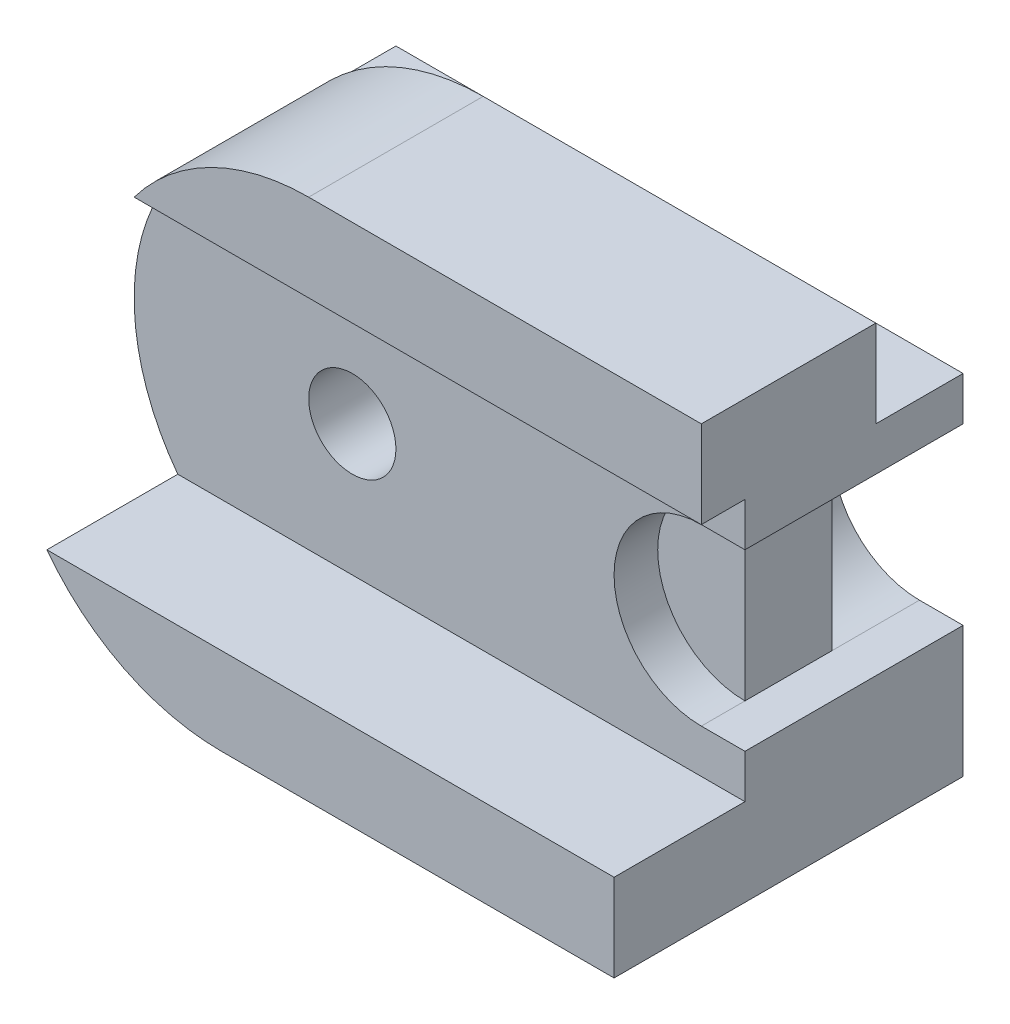
SolidWorks part; units mm, degrees
ref_plane "Front Plane" through (0, 0, 0) normal (0, 0, 1) x (1, 0, 0)
ref_plane "Top Plane" through (0, 0, 0) normal (0, 1, 0) x (1, 0, 0)
ref_plane "Right Plane" through (0, 0, 0) normal (1, 0, 0) x (0, 0, -1)
sketch "Sketch1" plane through (0, 0, 0) normal (0, 0, 1) x (1, 0, 0)
  line L0 (0, 50) -> (90, 50)
  line L1 (90, 50) -> (90, 20)
  line L2 (90, -20) -> (90, -50)
  line L3 (0, -50) -> (90, -50)
  line L4 (90, 20) -> (80, 20)
  line L5 (90, -20) -> (80, -20)
  arc A0 (0, 50) -> (0, -50) centre (0, 0) ccw
  arc A1 (80, 20) -> (80, -20) centre (80, 0) ccw
  dimension "D1" = 100
  dimension "D2" = 90
  dimension "D4" = 10
  dimension "D7" = 20
  dimension "D3" = 90
  dimension "D5" = 10
  dimension "D6" = 10
  dimension "D8" = 30
  dimension "D9" = 30
extrude "Boss-Extrude2" add sketch "Sketch1" along normal blind 80 contours A1 L4 L1 L0 A0 L3 L2 L5
sketch "Sketch8" plane through (90, 0, 0) normal (1, 0, 0) x (0, 0, -1)
  line L1 (0, 50) -> (-20, 50)
  line L2 (0, 50) -> (0, 30)
  line L3 (0, 30) -> (-20, 30)
  line L4 (-20, 50) -> (-20, 30)
  dimension "D1" = 20
  dimension "D2" = 20
extrude "Cut-Extrude5" cut sketch "Sketch8" against normal blind 205
ref_plane "Plane2" through (-50, 0, 0) normal (1, 0, 0) x (0, 0, -1)
sketch "Sketch9" plane through (-50, 0, 0) normal (1, 0, 0) x (0, 0, -1)
  line L1 (-80, 30) -> (-50, 30)
  line L2 (-80, 30) -> (-80, -30)
  line L3 (-80, -30) -> (-50, -30)
  line L4 (-50, 30) -> (-50, -30)
  dimension "D1" = 30
  dimension "D2" = 50
  dimension "D3" = 60
  dimension "D4" = 20
extrude "Cut-Extrude6" cut sketch "Sketch9" along normal blind 205
sketch "Sketch10" plane through (90, 0, 0) normal (1, 0, 0) x (0, 0, -1)
  line L1 (-80, 50) -> (-60, 50)
  line L2 (-80, 50) -> (-80, 30)
  line L3 (-80, 30) -> (-60, 30)
  line L4 (-60, 50) -> (-60, 30)
  dimension "D1" = 20
  dimension "D2" = 20
extrude "Cut-Extrude8" cut sketch "Sketch10" against normal blind 150
sketch "Sketch13" plane through (0, 0, 50) normal (0, 0, 1) x (1, 0, 0)
  circle A0 centre (0, 0) radius 10
  dimension "D1" = 20
extrude "Cut-Extrude9" cut sketch "Sketch13" against normal blind 150
sketch "Sketch14" plane through (0, 0, 0) normal (0, 0, -1) x (-1, 0, 0)
  line L0 (-90, -20) -> (-80, -20) construction
  line L1 (-80, 20) -> (-80, -20)
  arc A0 (-80, 20) -> (-80, -20) centre (-80, 0) cw
extrude "Boss-Extrude5" add sketch "Sketch14" against normal blind 40
sketch "Sketch15" plane through (0, 0, 0) normal (0, 0, -1) x (-1, 0, 0)
  line L0 (-80, 20) -> (-80, -20) construction
  line L1 (-80, 20) -> (-80, -20)
  arc A0 (-80, 20) -> (-80, -20) centre (-80, 0) cw
extrude "Cut-Extrude10" cut sketch "Sketch15" against normal blind 20
sketch "Sketch16" plane through (0, 0, 0) normal (0, 0, -1) x (-1, 0, 0)
  line L0 (-40, 30) -> (-0.001, 30)
  line L1 (40, 30) -> (-90, 30) construction
  line L2 (-0.001, 30) -> (0, 49.999)
  line L3 (-90, 30) -> (-90, 50) construction
  line L4 (-0.001, 30) -> (-0.001, -49.999)
  line L5 (-0.001, 30) -> (-0.001, 10)
  line L6 (0, -10) -> (-0.001, -49.999)
  line L7 (0, 49.999) -> (-0.001, -49.999)
  line L8 (-50, 0) -> (50, 0)
  circle A0 centre (0, 0) radius 50
  circle A1 centre (0, 0) radius 10
  arc A2 (-0.001, -49.999) -> (-49.999, 0) centre (0, 0) cw
  circle M1 centre (0, 0) radius 10
  line M8 (40, 30) -> (-90, 30)
  dimension "D1" = 100
  dimension "D7" = 20
  dimension "D2" = 39.999
  dimension "D3" = 19.999
  dimension "D4" = 90
  dimension "D5" = 79.999
  dimension "D6" = 89.999
  dimension "D8" = 20
extrude "Cut-Extrude15" cut sketch "Sketch16" against normal blind 20 contours A2 L4 L8 M1 | A0 L8 L4 M8 M1
sketch "Sketch18" plane through (0, -50, 0) normal (0, -1, 0) x (-1, 0, 0)
  line L1 (0, 0) -> (-10, 0)
  line L2 (0, 0) -> (0, -20)
  line L3 (0, -20) -> (-10, -20)
  line L4 (-10, 0) -> (-10, -20)
  dimension "D1" = 10
  dimension "D2" = 20
extrude "Cut-Extrude16" cut sketch "Sketch18" against normal blind 0.0001
